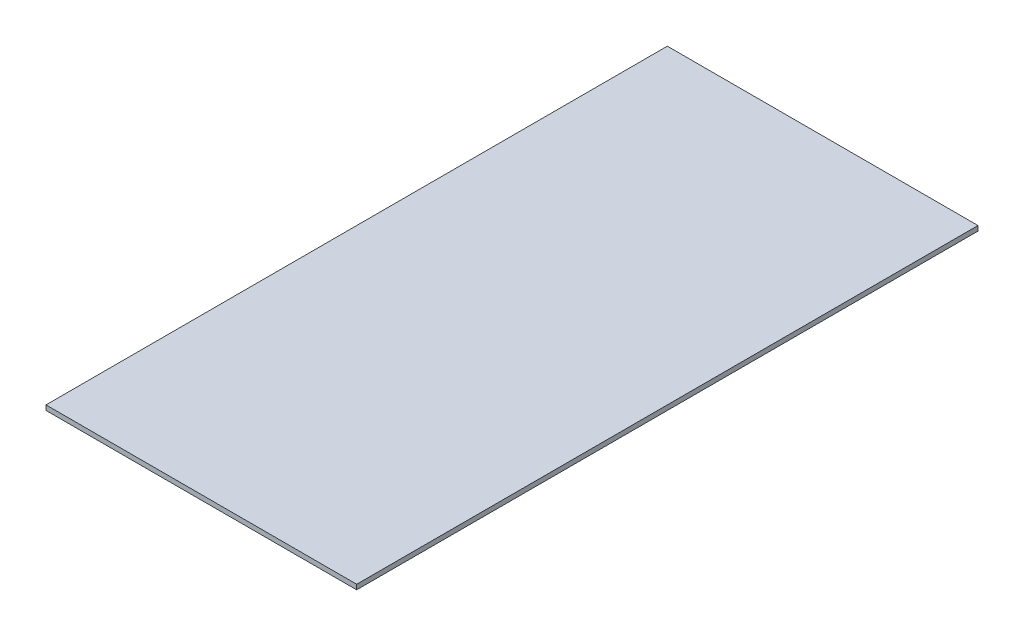
SolidWorks part; units mm, degrees
material "6063-T6"
ref_plane "Front Plane" through (0, 0, 0) normal (0, 0, 1) x (1, 0, 0)
ref_plane "Top Plane" through (0, 0, 0) normal (0, 1, 0) x (1, 0, 0)
ref_plane "Right Plane" through (0, 0, 0) normal (1, 0, 0) x (0, 0, -1)
sketch "Sketch1" plane through (0, 0, 0) normal (0, 1, 0) x (1, 0, 0)
  line L1 (0, 0) -> (-203.2, 0)
  line L2 (0, 0) -> (0, -406.4)
  line L3 (0, -406.4) -> (-203.2, -406.4)
  line L4 (-203.2, 0) -> (-203.2, -406.4)
  dimension "D1" = 406.4
  dimension "D2" = 203.2
extrude "Boss-Extrude1" add sketch "Sketch1" along normal blind 3.175
